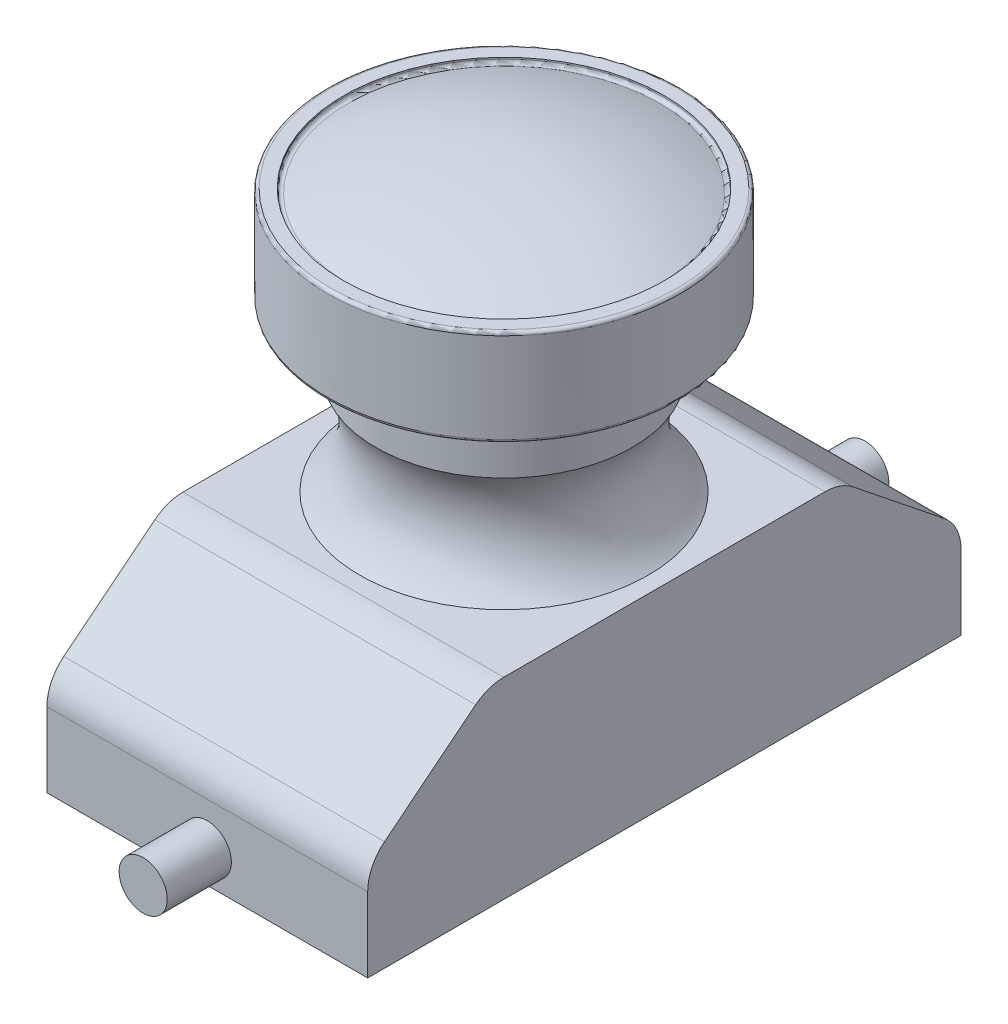
SolidWorks part; units mm, degrees
ref_plane "Front Plane" through (0, 0, 0) normal (0, 0, 1) x (1, 0, 0)
ref_plane "Top Plane" through (0, 0, 0) normal (0, 1, 0) x (1, 0, 0)
ref_plane "Right Plane" through (0, 0, 0) normal (1, 0, 0) x (0, 0, -1)
sketch "Sketch1" plane through (0, 0, 0) normal (1, 0, 0) x (0, 0, -1)
  line L0 (-9.25, 0) -> (9.25, 0)
  line L1 (-9.25, 0) -> (-9.25, 3)
  line L2 (-9.25, 3) -> (-5.5, 6)
  line L3 (-5.5, 6) -> (5.5, 6)
  line L4 (5.5, 6) -> (9.25, 3)
  line L5 (9.25, 3) -> (9.25, 0)
  line L6 (0, 0) -> (0, 9.9309) construction
  dimension "D1" = 18.5
  dimension "D2" = 3
  dimension "D3" = 3
  dimension "D4" = 11
extrude "Boss-Extrude1" add sketch "Sketch1" along normal mid plane 10
sketch "Sketch2" plane through (0, 0, 0) normal (1, 0, 0) x (0, 0, -1)
  line L0 (0, 6) -> (0, 14)
  line L1 (5.5, 6) -> (-5.5, 6) construction
  line L2 (0, 14) -> (5, 14)
  line L3 (5, 14) -> (5, 14.2)
  line L4 (5, 14.2) -> (5.5, 14.2)
  line L5 (5.5, 14.2) -> (5.5, 11.2)
  line L6 (5.5, 11.2) -> (4, 11.2)
  line L7 (4, 11.2) -> (4, 9.2)
  line L8 (0, 6) -> (4.5, 6)
  arc A0 (4, 9.2) -> (4.5, 6) centre (6.1318, 7.894) ccw
  dimension "D8" = 2.5
  dimension "D1" = 4.5
  dimension "D2" = 0.2
  dimension "D3" = 5
  dimension "D4" = 0.5
  dimension "D5" = 3
  dimension "D6" = 8
  dimension "D7" = 2
  dimension "D9" = 1.5
revolve "Revolve1" add sketch "Sketch2" angle 360 about L0
sketch "Sketch3" plane through (0, 0, 0) normal (1, 0, 0) x (0, 0, -1)
  line L0 (0, 14.2) -> (0, 15)
  line L1 (5, 14.2) -> (-5, 14.2) construction
  line L2 (0, 14.2) -> (0, 14)
  line L3 (0, 14) -> (-5, 14)
  arc A0 (0, 15) -> (-5, 14) centre (-0.2003, 3.0017) ccw
  dimension "D3" = 12
  dimension "D1" = 0.8
  dimension "D2" = 0.2
  dimension "D4" = 5
revolve "Revolve2" add sketch "Sketch3" angle 360 about L0
fillet "Fillet1" radius 0.1 2 edges at (0, 11.2, -5.5) (0, 14.2, -5.5)
fillet "Fillet2" radius 0.1 1 edges at (0, 14, -5)
fillet "Fillet3" radius 1.4 4 edges at (0, 3, 9.25) (0, 6, 5.5) (0, 6, -5.5) (0, 3, -9.25)
sketch "Sketch4" plane through (0, 0, -9.25) normal (0, 0, -1) x (-1, 0, 0)
  circle A0 centre (0, 1) radius 0.75
  dimension "D2" = 1.5
  dimension "D1" = 1
extrude "Boss-Extrude2" add sketch "Sketch4" along normal blind 2
mirror "Mirror1" about plane through (0, 0, 0) normal (0, 0, 1) of "Boss-Extrude2"
